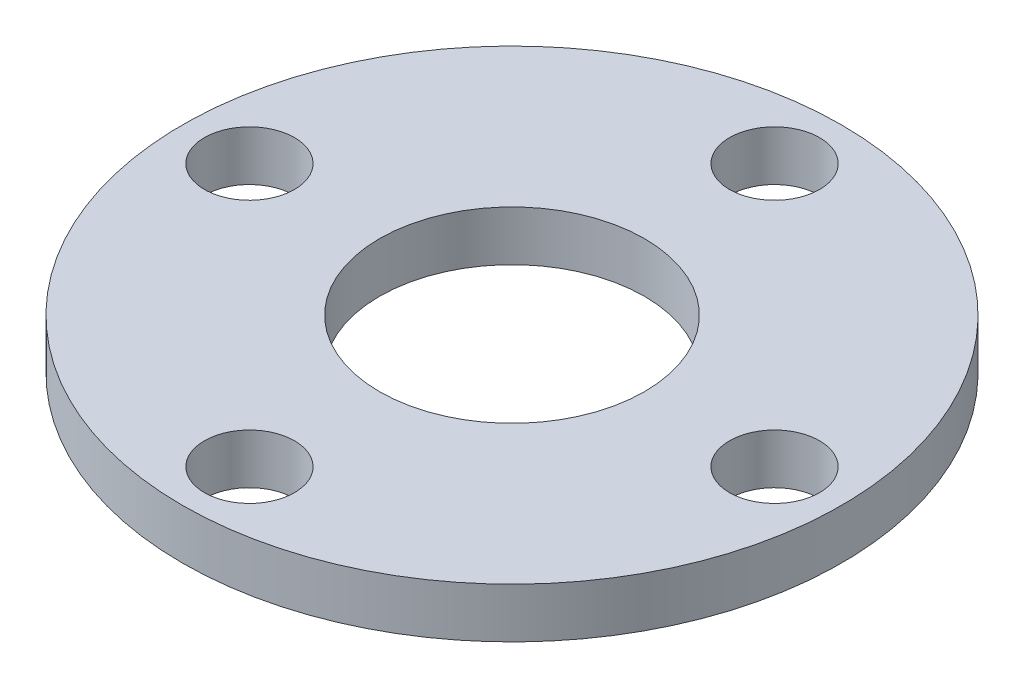
SolidWorks part; units mm, degrees
ref_plane "Alzado" through (0, 0, 0) normal (0, 0, 1) x (1, 0, 0)
ref_plane "Planta" through (0, 0, 0) normal (0, 1, 0) x (1, 0, 0)
ref_plane "Vista lateral" through (0, 0, 0) normal (1, 0, 0) x (0, 0, -1)
sketch "Croquis1" plane through (0, 0, 0) normal (0, 1, 0) x (1, 0, 0)
  circle A0 centre (0, 0) radius 13.18
  circle A1 centre (0, 0) radius 5.3
  dimension "D1" = 26.36
  dimension "D2" = 10.6
extrude "Saliente-Extruir1" add sketch "Croquis1" along normal blind 2
sketch "Croquis2" plane through (0, 2, 0) normal (0, 1, 0) x (1, 0, 0)
  line L0 (0, 0) -> (13.18, 0) construction
  circle A0 centre (0, 0) radius 13.18 construction
  circle A1 centre (0, 0) radius 10.5 construction
  circle A2 centre (10.5, 0) radius 1.8
  dimension "D1" = 3.6
  dimension "D2" = 21
extrude "Cortar-Extruir1" cut sketch "Croquis2" against normal blind 2
pattern_circular "MatrizC1" count 4 over 360 about axis through (0, 0, 0) along (0, 1, 0) of "Cortar-Extruir1"
